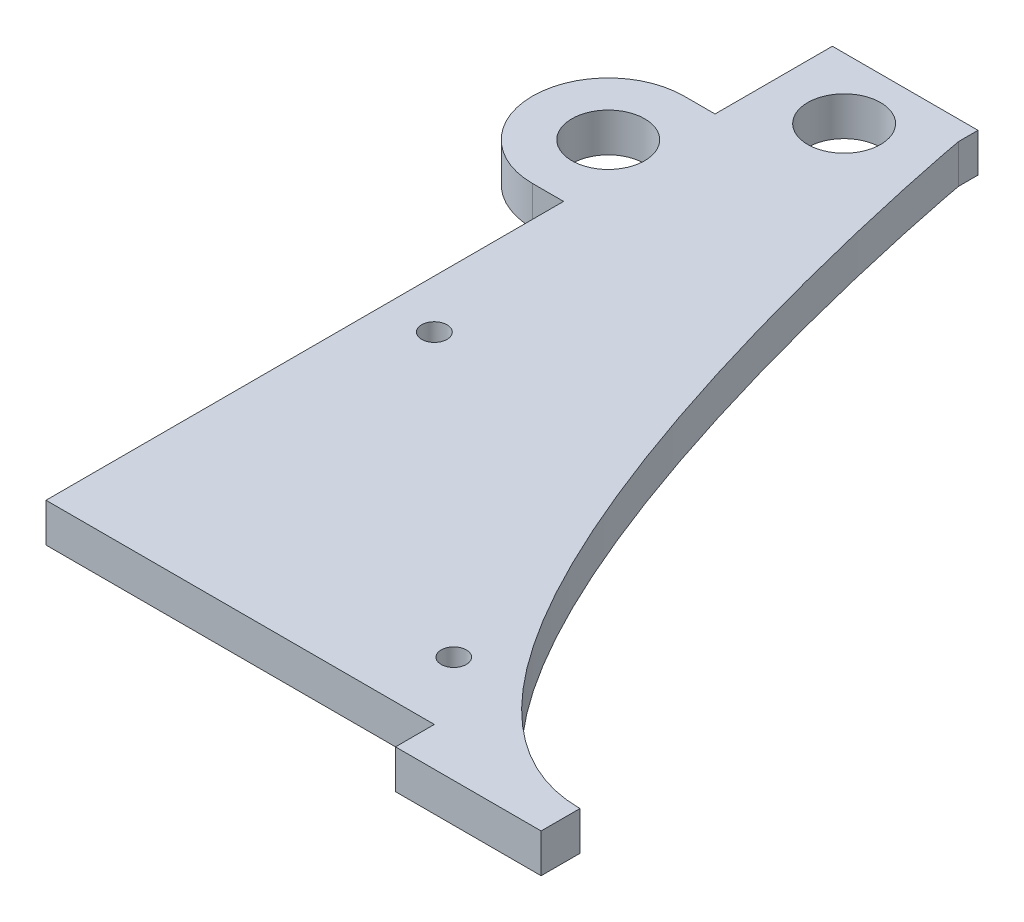
SolidWorks part; units mm, degrees
ref_plane "Front Plane" through (0, 0, 0) normal (0, 0, 1) x (1, 0, 0)
ref_plane "Top Plane" through (0, 0, 0) normal (0, 1, 0) x (1, 0, 0)
ref_plane "Right Plane" through (0, 0, 0) normal (1, 0, 0) x (0, 0, -1)
sketch "Sketch1" plane through (0, 0, 0) normal (0, 1, 0) x (1, 0, 0)
  line L0 (9.525, -53.975) -> (60.325, -53.975) construction
  line L1 (-9.525, -53.975) -> (9.525, -53.975) construction
  line L2 (-9.525, -53.975) -> (-9.525, 53.975) construction
  line L3 (-9.525, 53.975) -> (9.525, 53.975)
  line L4 (9.525, -53.975) -> (9.525, 53.975) construction
  line L5 (-9.525, -53.975) -> (9.525, 53.975) construction
  line L6 (-9.525, 53.975) -> (9.525, -53.975) construction
  line L7 (0, 53.975) -> (0, 45.9867) construction
  line L8 (-9.525, 50.7492) -> (9.525, 50.7492) construction
  line L9 (9.525, 51.435) -> (9.525, 53.975)
  line L10 (60.325, -53.975) -> (60.325, -48.895) construction
  line L11 (60.325, -48.895) -> (-9.525, -48.895) construction
  line L12 (60.325, -53.975) -> (60.325, -48.895) construction
  line L13 (60.325, -48.895) -> (-9.525, -48.895)
  line L14 (-9.525, -48.895) -> (-9.525, 53.975)
  line L15 (31.115, -19.685) -> (31.115, -48.895) construction
  circle A0 centre (0, 45.9867) radius 4.7625
  spline S0 degree 3 poles (9.525, 51.435) (9.525, 51.2145) (27.8191, -48.895) (60.325, -48.895) knots 0 0 0 0 1 1 1 1
  point P4 (0, 0)
  dimension "D5" = 9.525
  dimension "D1" = 107.95
  dimension "D2" = 19.05
  dimension "D3" = 50.8
  dimension "D4" = 2.54
  dimension "D6" = 104.7242
  dimension "D7" = 5.08
  dimension "D8" = 40.64
  dimension "D9" = 29.21
extrude "Boss-Extrude1" add sketch "Sketch1" along normal blind 5.08
sketch "Sketch4" plane through (0, 5.08, 0) normal (0, 1, 0) x (1, 0, 0)
  line L0 (-9.525, 53.975) -> (-9.525, -48.895) construction
  line L1 (60.325, -48.895) -> (41.275, -48.895)
  line L2 (60.325, -48.895) -> (60.325, -53.975)
  line L3 (60.325, -53.975) -> (41.275, -53.975)
  line L4 (41.275, -48.895) -> (41.275, -53.975)
  line L5 (60.325, -48.895) -> (41.275, -53.975) construction
  line L6 (60.325, -53.975) -> (41.275, -48.895) construction
  point P4 (50.8, -51.435)
  dimension "D1" = 50.8
  dimension "D2" = 5.08
extrude "Boss-Extrude2" add sketch "Sketch4" against normal up to surface (5.08 mm away) up to face at (17.145, 0, -2.286)
sketch "Sketch5" plane through (0, 0, 0) normal (0, -1, 0) x (1, 0, 0)
  circle A1 centre (34.925, 40.005) radius 1.651
  circle A3 centre (-3.175, 4.445) radius 1.6607
extrude "Cut-Extrude1" cut sketch "Sketch5" against normal through all both
sketch "Sketch6" plane through (0, 0, 0) normal (0, -1, 0) x (1, 0, 0)
  line L0 (-9.525, -28.7203) -> (-13.589, -28.7203) construction
  line L1 (-9.525, -53.975) -> (-9.525, 48.895) construction
  line L2 (-13.589, -18.8143) -> (-9.525, -18.8143)
  line L3 (-13.589, -38.6263) -> (-9.525, -38.6263)
  line L4 (-9.525, -18.8143) -> (-9.525, -19.6863)
  line L5 (-9.525, -38.6263) -> (-9.525, -37.7543)
  circle A0 centre (-13.589, -28.7203) radius 4.7625
  arc A1 (-9.525, -37.7543) -> (-9.525, -19.6863) centre (-13.589, -28.7203) ccw
  arc A2 (-13.589, -18.8143) -> (-13.589, -38.6263) centre (-13.589, -28.7203) ccw
  dimension "D1" = 9.525
  dimension "D3" = 19.812
  dimension "D2" = 4.064
extrude "Boss-Extrude3" add sketch "Sketch6" against normal blind 5.08
sketch "Sketch8" plane through (0, 5.08, 0) normal (0, 1, 0) x (1, 0, 0)
  circle A0 centre (-13.589, 28.7203) radius 4.7625
extrude "Cut-Extrude2" cut sketch "Sketch8" against normal through all
